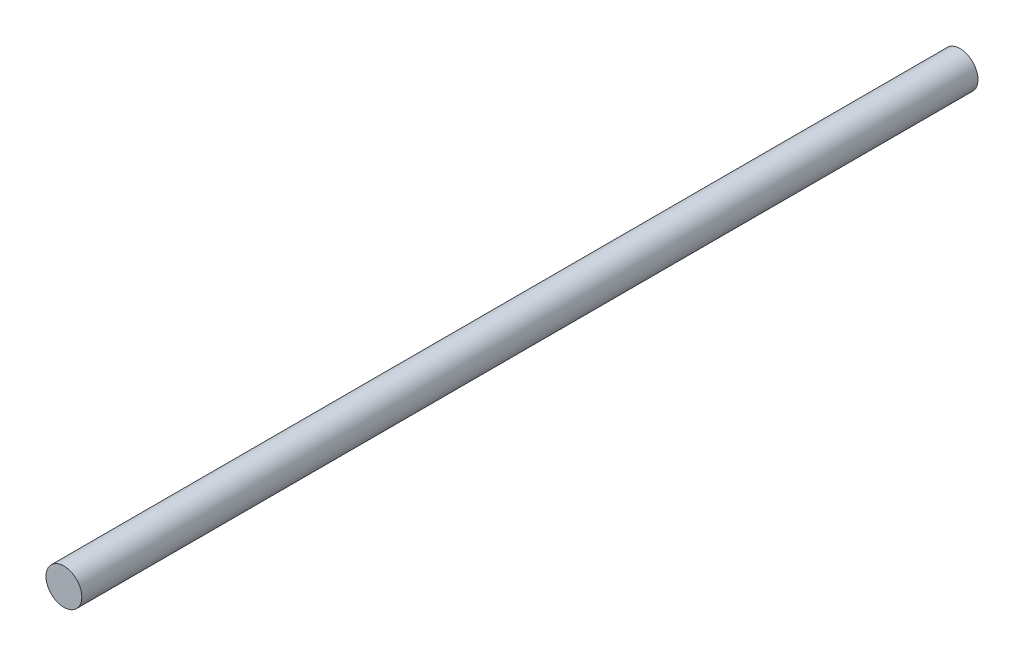
SolidWorks part; units mm, degrees
ref_plane "前视基准面" through (0, 0, 0) normal (0, 0, 1) x (1, 0, 0)
ref_plane "上视基准面" through (0, 0, 0) normal (0, 1, 0) x (1, 0, 0)
ref_plane "右视基准面" through (0, 0, 0) normal (1, 0, 0) x (0, 0, -1)
sketch "草图1" plane through (0, 0, 0) normal (0, 0, 1) x (1, 0, 0)
  circle A0 centre (0, 0) radius 4
  dimension "D1" = 8
extrude "凸台-拉伸1" add sketch "草图1" along normal mid plane 200
